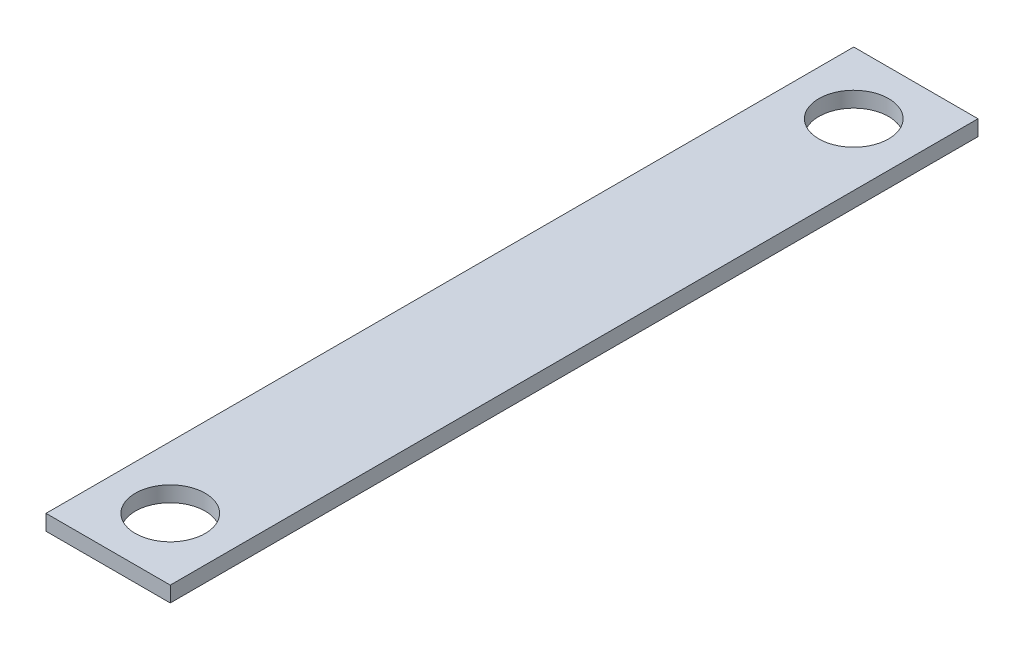
SolidWorks part; units mm, degrees
ref_plane "Front Plane" through (0, 0, 0) normal (0, 0, 1) x (1, 0, 0)
ref_plane "Top Plane" through (0, 0, 0) normal (0, 1, 0) x (1, 0, 0)
ref_plane "Right Plane" through (0, 0, 0) normal (1, 0, 0) x (0, 0, -1)
sketch "Sketch1" plane through (0, 0, 0) normal (0, 1, 0) x (1, 0, 0)
  line L0 (25.4, 0) -> (25.4, 25.4)
  line L1 (0, 0) -> (50.8, 0)
  line L2 (0, 0) -> (0, 330.2)
  line L3 (0, 330.2) -> (50.8, 330.2)
  line L4 (50.8, 0) -> (50.8, 330.2)
  circle A1 centre (25.4, 25.4) radius 14.2748
  circle A2 centre (25.4, 304.8) radius 14.2748
  dimension "D3" = 28.5496
  dimension "D4" = 25.4
  dimension "D1" = 50.8
  dimension "D2" = 330.2
extrude "Boss-Extrude2" add sketch "Sketch1" along normal blind 6.35
